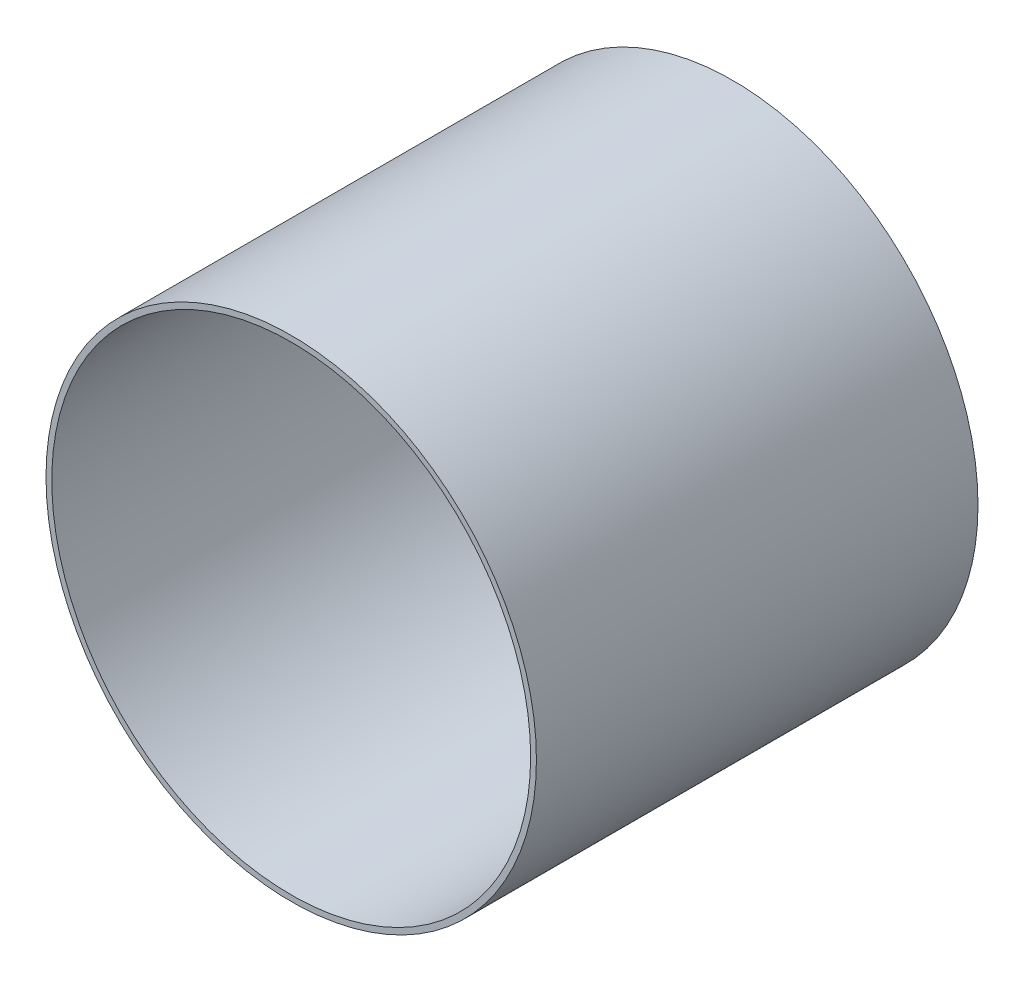
SolidWorks part; units mm, degrees
ref_plane "Front Plane" through (0, 0, 0) normal (0, 0, 1) x (1, 0, 0)
ref_plane "Top Plane" through (0, 0, 0) normal (0, 1, 0) x (1, 0, 0)
ref_plane "Right Plane" through (0, 0, 0) normal (1, 0, 0) x (0, 0, -1)
sketch "Sketch1" plane through (0, 0, 0) normal (0, 0, 1) x (1, 0, 0)
  circle A0 centre (0, 0) radius 63.4746
  circle A1 centre (0, 0) radius 61.976
  dimension "D1" = 123.952
  dimension "D2" = 126.9492
extrude "Boss-Extrude1" add sketch "Sketch1" along normal mid plane 114.3
equation "\"AIRFRAME_OD\"= 5.15in"
equation "\"AIRFRAME_ID\"= 5.00in"
equation "\"FLAT_T\"= 0.125in"
equation "\"NOSE_EXP_L\"= 27in"
equation "\"NOSE_SHOULDER_L\"= 5in"
equation "\"MAIN_L\"= 30in"
equation "\"RECO_COUP_L\"= 10in"
equation "\"RECO_SWITCH_L\"= 2in"
equation "\"DROGUE_L\"= 20in"
equation "\"ATS_FORE_COUP_L\"= 5.5in"
equation "\"ATS_AFT_COUP_L\"= 4.5in"
equation "\"LOWER_L\"= 30in"
equation "\"FIN_N\"= 4"
equation "\"CR_AFT_X\"= 0.5in"
equation "\"CR_FORE_X\"= 9.25in"
equation "\"D1@Sketch1\"=\"COUPLER_ID\""
equation "\"D2@Sketch1\"=\"COUPLER_OD\""
equation "\"D1@Boss-Extrude1\"=\"ATS_AFT_COUP_L\""
equation "\"FIN_ROOT\"= 8in"
equation "\"FIN_X\"= 0.75in"
equation "\"MOTOR_OD\"= 3.091in"
equation "\"MOTOR_ID\"= 3.00in"
equation "\"COUPLER_OD\"= 4.998in"
equation "\"COUPLER_ID\"= 4.88in"
equation "\"RECO_ROD_X\"= 3.5in"
equation "\"ATS_ROD_X\"= 3.75in"
equation "\"MOTOR_L\"= 14in"
equation "\"MOTOR_LOWER_X\"= 2in"
